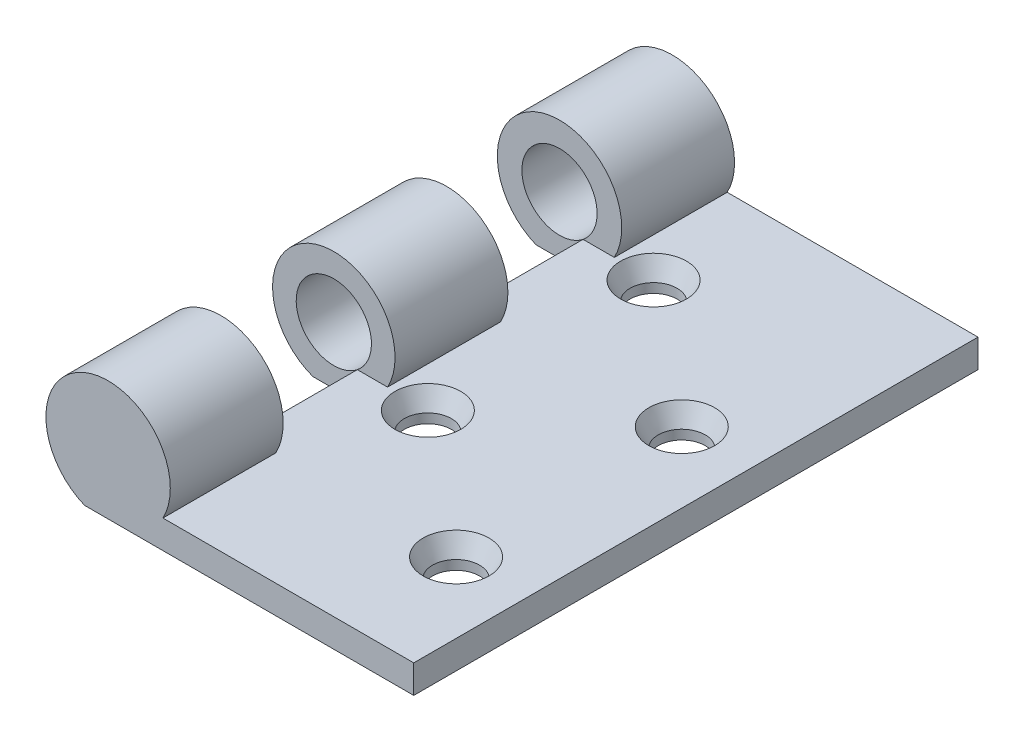
SolidWorks part; units mm, degrees
ref_plane "Front Plane" through (0, 0, 0) normal (0, 0, 1) x (1, 0, 0)
ref_plane "Top Plane" through (0, 0, 0) normal (0, 1, 0) x (1, 0, 0)
ref_plane "Right Plane" through (0, 0, 0) normal (1, 0, 0) x (0, 0, -1)
sketch "Sketch1" plane through (0, 0, 0) normal (0, 1, 0) x (1, 0, 0)
  line L1 (15, -30) -> (-15, -30)
  line L2 (15, -30) -> (15, 30)
  line L3 (15, 30) -> (-15, 30)
  line L4 (-15, -30) -> (-15, 30)
  line L5 (15, -30) -> (-15, 30) construction
  line L6 (15, 30) -> (-15, -30) construction
  point P0 (0, 0)
  dimension "D1" = 30
  dimension "D2" = 60
extrude "Boss-Extrude1" add sketch "Sketch1" along normal blind 3
sketch "Sketch2" plane through (0, 0, 30) normal (0, 0, 1) x (1, 0, 0)
  line L0 (-15, 0) -> (-20, 0)
  line L1 (-15, 3) -> (-15, 0) construction
  circle A0 centre (-17.5, 6.1225) radius 4
  arc A1 (-15, 0) -> (-20, 0) centre (-17.5, 6.1225) ccw
  dimension "D1" = 8
  dimension "D2" = 2.5
extrude "Boss-Extrude2" add sketch "Sketch2" against normal blind 12
mirror "Mirror1" about plane through (0, 0, 0) normal (0, 0, 1) of "Boss-Extrude2"
sketch "Sketch3" plane through (0, 0, 0) normal (0, 0, 1) x (1, 0, 0)
  line L0 (-19.7215, 0) -> (-15.2785, 0)
  line L1 (-20, 0) -> (15, 0) construction
  circle A0 centre (-17.5, 6.1225) radius 4
  arc A1 (-15.2785, 0) -> (-19.7215, 0) centre (-17.5, 6.1225) ccw
extrude "Boss-Extrude3" add sketch "Sketch3" along normal mid plane 12
sketch "Sketch8" plane through (0, 3, 0) normal (0, 1, 0) x (1, 0, 0)
  line L0 (7.5, 30) -> (7.5, -30) construction
  line L1 (15, 30) -> (-11.6703, 30) construction
  line L2 (-11.6703, -30) -> (15, -30) construction
  line L3 (7.5, -30) -> (-7.5, -30) construction
  line L4 (-7.5, -30) -> (-7.5, 30) construction
  line L5 (15, -30) -> (15, 30) construction
  circle A1 centre (7.5, -18) radius 2.5
  circle A4 centre (-7.5, -6) radius 2.5
  circle A5 centre (7.5, 6) radius 2.5
  circle A6 centre (-7.5, 18) radius 2.5
  dimension "D3" = 5
  dimension "D1" = 7.5
  dimension "D2" = 15
  dimension "D4" = 12
  dimension "D5" = 12
  dimension "D6" = 12
  dimension "D7" = 12
extrude "Cut-Extrude1" cut sketch "Sketch8" against normal through all
chamfer "Chamfer1" distance 1 distance2 2 4 edges at (7.5, 3, 20.5) (7.5, 3, -3.5) (-7.5, 3, -15.5) (-7.5, 3, 8.5)
sketch "Sketch9" plane through (0, 0, 30) normal (0, 0, 1) x (1, 0, 0)
  circle A0 centre (-17.5, 6.1225) radius 4 construction
  circle A1 centre (-17.5, 6.1225) radius 4
extrude "Boss-Extrude4" add sketch "Sketch9" against normal blind 2
